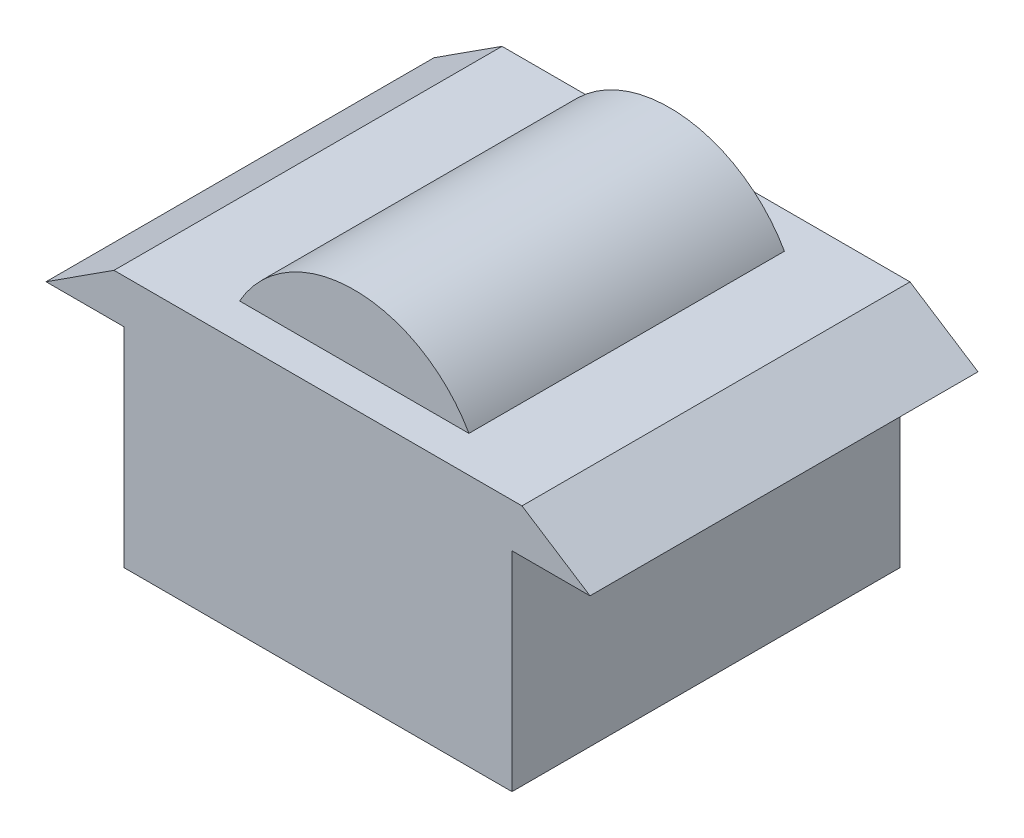
SolidWorks part; units mm, degrees
material "Nylon 101"
ref_plane "Front Plane" through (0, 0, 0) normal (0, 0, 1) x (1, 0, 0)
ref_plane "Top Plane" through (0, 0, 0) normal (0, 1, 0) x (1, 0, 0)
ref_plane "Right Plane" through (0, 0, 0) normal (1, 0, 0) x (0, 0, -1)
sketch "Sketch1" plane through (0, 0, 0) normal (0, 0, 1) x (1, 0, 0)
  line L0 (0, 38.5729) -> (0, -39.8293) construction
  line L1 (-23.3699, 7.407) -> (-13.137, 7.407)
  line L2 (23.3699, 7.407) -> (31.1599, 2.3813)
  line L3 (31.1599, 2.3813) -> (22.225, 2.3812)
  line L4 (22.225, 2.3812) -> (22.225, -21.5187)
  line L5 (22.225, -21.5187) -> (-22.225, -21.5187)
  line L6 (0, 15.0813) -> (38.1959, 15.0812) construction
  line L7 (-22.225, 2.3812) -> (-22.225, -21.5187)
  line L8 (-31.1599, 2.3813) -> (-22.225, 2.3812)
  line L9 (-23.3699, 7.407) -> (-31.1599, 2.3813)
  line L10 (13.137, 7.407) -> (23.3699, 7.407)
  arc A0 (13.137, 7.407) -> (-13.137, 7.407) centre (0, 0) ccw
  point P14 (0, -21.5188)
  point P17 (0, 7.407)
  dimension "D1" = 36.6
  dimension "D3" = 30.1625
  dimension "D2" = 12.7
  dimension "D4" = 22.225
extrude "Boss-Extrude1" add sketch "Sketch1" along normal mid plane 44.45
sketch "Sketch2" plane through (0, 7.407, 0) normal (0, 1, 0) x (1, 0, 0)
  line L0 (0, 0) -> (49.4134, 0) construction
  line L1 (-13.137, -22.225) -> (-13.137, 22.225) construction
  line L2 (13.137, 22.225) -> (-13.137, 22.225)
  line L3 (13.137, 22.225) -> (13.137, 18.0704)
  line L4 (13.137, 18.0704) -> (-13.137, 18.0704)
  line L5 (-13.137, 22.225) -> (-13.137, 18.0704)
  line L6 (-13.137, -22.225) -> (-13.137, -18.0704)
  line L7 (13.137, -18.0704) -> (-13.137, -18.0704)
  line L8 (13.137, -22.225) -> (13.137, -18.0704)
  line L9 (13.137, -22.225) -> (-13.137, -22.225)
extrude "Cut-Extrude1" cut sketch "Sketch2" along normal blind 44.45
